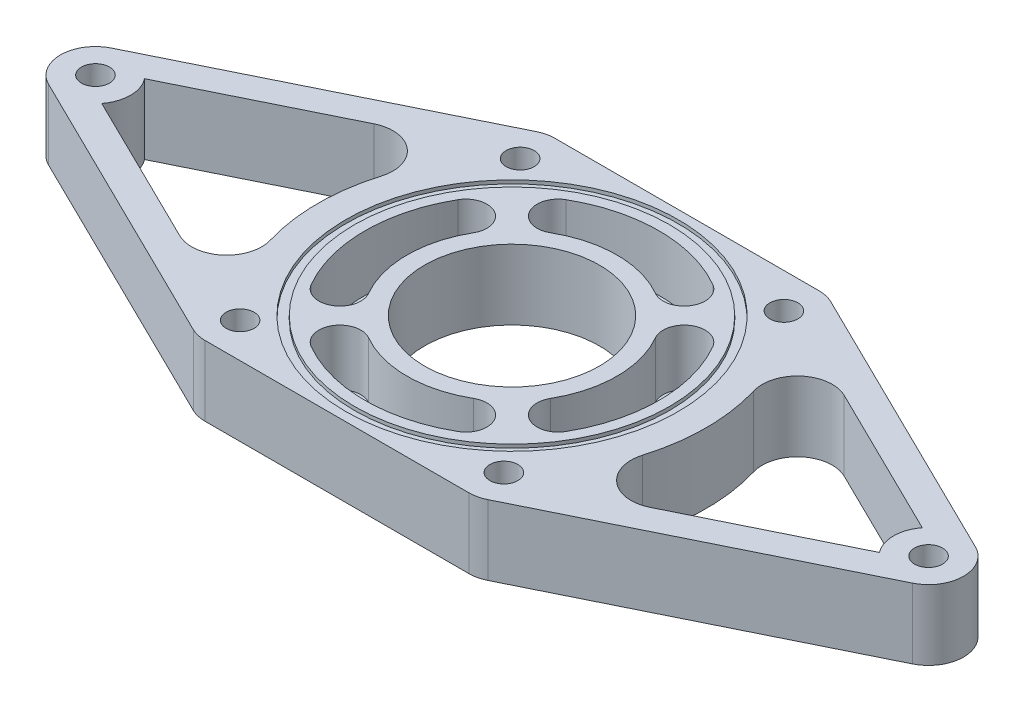
SolidWorks part; units mm, degrees
material "AISI 1020"
ref_plane "Front Plane" through (0, 0, 0) normal (0, 0, 1) x (1, 0, 0)
ref_plane "Top Plane" through (0, 0, 0) normal (0, 1, 0) x (1, 0, 0)
ref_plane "Right Plane" through (0, 0, 0) normal (1, 0, 0) x (0, 0, -1)
sketch "Sketch1" plane through (0, 0, 0) normal (0, 1, 0) x (1, 0, 0)
  line L0 (0, 0) -> (0, 71.4424) construction
  line L1 (-40, -50) -> (40, -50)
  line L3 (-40, 50) -> (40, 50)
  line L5 (-40, -50) -> (40, 50) construction
  line L6 (-40, 50) -> (40, -50) construction
  line L7 (-123.4135, 8.9733) -> (-40, 50)
  line L8 (-123.4135, -8.9733) -> (-40, -50)
  line L9 (40, -50) -> (123.4135, -8.9733)
  line L10 (123.4135, 8.9733) -> (40, 50)
  line L11 (0, 0) -> (-54.9584, 0) construction
  arc A0 (-123.4135, 8.9733) -> (-123.4135, -8.9733) centre (-119, 0) ccw
  arc A1 (123.4135, -8.9733) -> (123.4135, 8.9733) centre (119, 0) ccw
  point P0 (0, 0)
  dimension "D3" = 10
  dimension "D1" = 80
  dimension "D2" = 100
  dimension "D4" = 238
extrude "Boss-Extrude1" add sketch "Sketch1" along normal blind 20
sketch "Sketch2" plane through (0, 20, 0) normal (0, 1, 0) x (1, 0, 0)
  circle A0 centre (0, 0) radius 47.5
  circle A1 centre (0, 0) radius 45
  dimension "D1" = 95
  dimension "D2" = 90
extrude "Cut-Extrude1" cut sketch "Sketch2" against normal blind 1
sketch "Sketch3" plane through (0, 20, 0) normal (0, 1, 0) x (1, 0, 0)
  line L1 (0, 0) -> (77.5866, 0) construction
  arc A0 (31.1769, 18) -> (31.1769, -18) centre (0, 0) cw construction
  arc A1 (36.3731, -21) -> (36.3731, 21) centre (0, 0) ccw
  arc A2 (25.9808, -15) -> (25.9808, 15) centre (0, 0) ccw
  arc A3 (25.9808, -15) -> (36.3731, -21) centre (31.1769, -18) ccw
  arc A4 (36.3731, 21) -> (25.9808, 15) centre (31.1769, 18) ccw
  point P5 (36, 0)
  dimension "D1" = 6
  dimension "D3" = 36
  dimension "D2" = 60
extrude "Cut-Extrude2" cut sketch "Sketch3" against normal blind 16
pattern_circular "CirPattern1" count 4 over 360 about axis through (0, 0, 0) along (0, 1, 0) of "Cut-Extrude2"
sketch "Sketch4" plane through (0, 20, 0) normal (0, 1, 0) x (1, 0, 0)
  circle A0 centre (0, 0) radius 25
  dimension "D1" = 50
extrude "Cut-Extrude3" cut sketch "Sketch4" against normal through all
sketch "Sketch6" plane through (0, 20, 0) normal (0, 1, 0) x (1, 0, 0)
  circle A0 centre (-119, 0) radius 4
  circle A1 centre (119, 0) radius 4
  dimension "D1" = 8
  dimension "D2" = 8
extrude "Cut-Extrude4" cut sketch "Sketch6" against normal through all
sketch "Sketch8" plane through (0, 20, 0) normal (0, 1, 0) x (1, 0, 0)
  line L0 (-67.1736, 27.7194) -> (-111.0907, 6.119)
  line L1 (-111.0907, -6.119) -> (-67.1736, -27.7194)
  line L2 (-123.4135, -8.9733) -> (-40, -50) construction
  line L3 (-40, 50) -> (-123.4135, 8.9733) construction
  arc A0 (-53.1784, 15.8841) -> (-53.1784, -15.8841) centre (0, 0) ccw
  arc A1 (-111.0907, -6.119) -> (-111.0907, 6.119) centre (-119, 0) ccw
  arc A2 (-67.1736, -27.7194) -> (-53.1784, -15.8841) centre (-62.7601, -18.7461) ccw
  arc A3 (-67.1736, 27.7194) -> (-53.1784, 15.8841) centre (-62.7601, 18.7461) cw
  dimension "D1" = 55.5
  dimension "D4" = 10
  dimension "D5" = 10
  dimension "D2" = 8
  dimension "D3" = 8
extrude "Cut-Extrude5" cut sketch "Sketch8" against normal through all
mirror "Mirror1" about plane through (0, 0, 0) normal (1, 0, 0) of "Cut-Extrude5"
fillet "Fillet1" radius 10 4 edges at (-40, 10, -50) (40, 10, -50) (40, 10, 50) (-40, 10, 50)
sketch "Sketch9" plane through (0, 20, 0) normal (0, 1, 0) x (1, 0, 0)
  circle A0 centre (-37.6738, 40) radius 4
  circle A1 centre (37.6738, 40) radius 4
  circle A2 centre (-37.6738, -40) radius 4
  circle A3 centre (37.6738, -40) radius 4
  dimension "D1" = 8
extrude "Cut-Extrude6" cut sketch "Sketch9" against normal through all
